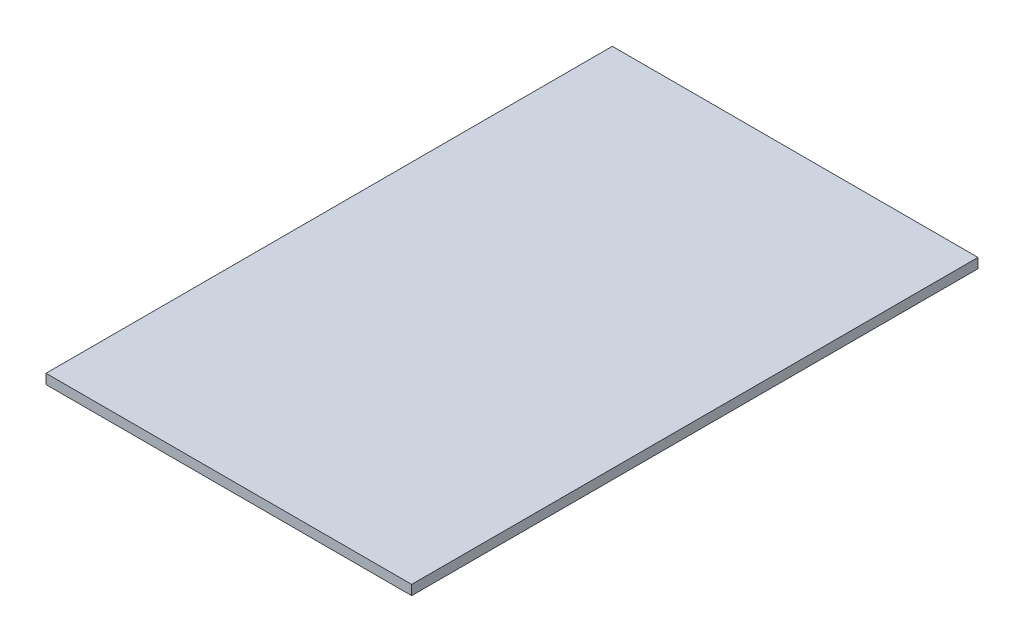
SolidWorks part; units mm, degrees
material "Glass"
ref_plane "Front Plane" through (0, 0, 0) normal (0, 0, 1) x (1, 0, 0)
ref_plane "Top Plane" through (0, 0, 0) normal (0, 1, 0) x (1, 0, 0)
ref_plane "Right Plane" through (0, 0, 0) normal (1, 0, 0) x (0, 0, -1)
sketch "Sketch1" plane through (0, 0, 0) normal (0, 1, 0) x (1, 0, 0)
  line L1 (-20.5, 31.75) -> (20.5, 31.75)
  line L2 (-20.5, 31.75) -> (-20.5, -31.75)
  line L3 (-20.5, -31.75) -> (20.5, -31.75)
  line L4 (20.5, 31.75) -> (20.5, -31.75)
  line L5 (-20.5, 31.75) -> (20.5, -31.75) construction
  line L6 (-20.5, -31.75) -> (20.5, 31.75) construction
  point P0 (0, 0)
  dimension "D1" = 41
  dimension "D2" = 63.5
extrude "Boss-Extrude1" add sketch "Sketch1" along normal blind 1.1
